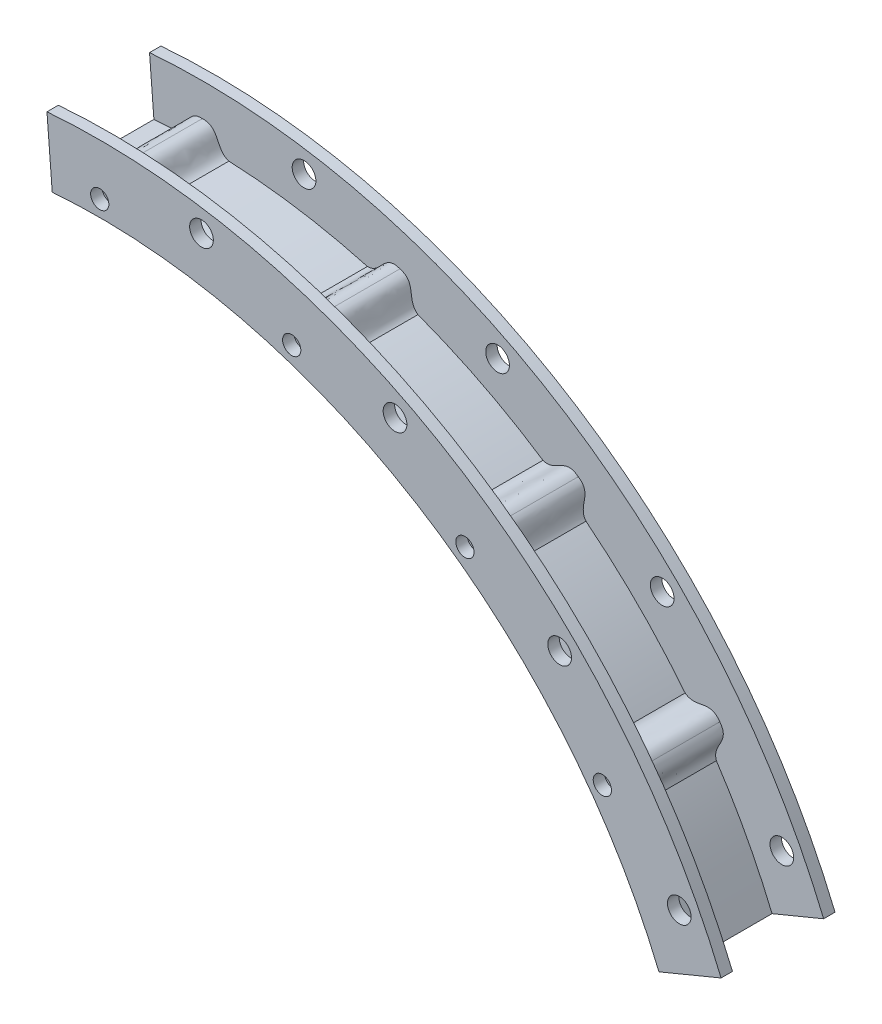
SolidWorks part; units mm, degrees
material "Maple"
ref_plane "Wasteboard" through (0, 0, 0) normal (0, 0, 1) x (1, 0, 0)
ref_plane "Left-Right" through (0, 0, 0) normal (0, 1, 0) x (1, 0, 0)
ref_plane "Front-Back" through (0, 0, 0) normal (1, 0, 0) x (0, 0, -1)
sketch "Sketch2" plane through (0, 0, 0) normal (0, 0, 1) x (1, 0, 0)
  circle A0 centre (0, 0) radius 192.0875 construction
  circle A1 centre (0, 0) radius 209.55 construction
  circle A2 centre (0, 0) radius 171.831 construction
  circle A3 centre (0, 0) radius 252.73 construction
  circle A4 centre (0, 0) radius 184.531 construction
  circle A5 centre (0, 0) radius 187.3885
  circle A6 centre (0, 0) radius 168.656
  dimension "D1" = 384.175
  dimension "D2" = 419.1
  dimension "D3" = 343.662
  dimension "D4" = 505.46
  dimension "D5" = 369.062
  dimension "D6" = 374.777
  dimension "D7" = 337.312
extrude "Boss-Extrude1" add sketch "Sketch2" along normal blind 3.175
sketch "Sketch3" plane through (0, 0, 3.175) normal (0, 0, 1) x (1, 0, 0)
  circle A0 centre (0, 0) radius 171.831
  circle A1 centre (0, 0) radius 168.656
  dimension "D1" = 343.662
extrude "Boss-Extrude2" add sketch "Sketch3" along normal blind 25.4
sketch "Sketch4" plane through (0, 0, 28.575) normal (0, 0, 1) x (1, 0, 0)
  circle A0 centre (0, 0) radius 187.3885
  circle A1 centre (0, 0) radius 168.656
extrude "Boss-Extrude3" add sketch "Sketch4" along normal blind 3.175
sketch "Sketch5" plane through (0, 0, 31.75) normal (0, 0, 1) x (1, 0, 0)
  line L0 (0, 0) -> (0, 196.8159) construction
  line L1 (-7.405, 171.6714) -> (7.405, 171.6714)
  line L2 (0, 178.2342) -> (22.1091, 178.2342) construction
  line L3 (50.9118, 162.6825) -> (45.3645, 143.4767) construction
  line L4 (46.0068, 165.5574) -> (60.092, 160.9809)
  line L5 (94.9151, 143.2376) -> (106.8967, 134.5325)
  line L6 (134.5325, 106.8967) -> (143.2376, 94.9151)
  line L7 (160.9809, 60.092) -> (165.5574, 46.0068)
  line L8 (171.6714, 7.405) -> (171.6714, -7.405)
  line L9 (165.5574, -46.0068) -> (160.9809, -60.092)
  line L10 (143.2376, -94.9151) -> (134.5325, -106.8967)
  line L11 (106.8967, -134.5325) -> (94.9151, -143.2376)
  line L12 (60.092, -160.9809) -> (46.0068, -165.5574)
  line L13 (7.405, -171.6714) -> (-7.405, -171.6714)
  line L14 (-46.0068, -165.5574) -> (-60.092, -160.9809)
  line L15 (-94.9151, -143.2376) -> (-106.8967, -134.5325)
  line L16 (-134.5325, -106.8967) -> (-143.2376, -94.9151)
  line L17 (-160.9809, -60.092) -> (-165.5574, -46.0068)
  line L18 (-171.6714, -7.405) -> (-171.6714, 7.405)
  line L19 (-165.5574, 46.0068) -> (-160.9809, 60.092)
  line L20 (-143.2376, 94.9151) -> (-134.5325, 106.8967)
  line L21 (-106.8967, 134.5325) -> (-94.9151, 143.2376)
  line L22 (-60.092, 160.9809) -> (-46.0068, 165.5574)
  circle A0 centre (0, 0) radius 171.831 construction
  circle A1 centre (0, 173.101) radius 1.27
  circle A3 centre (53.4912, 164.6288) radius 1.27
  circle A4 centre (101.7462, 140.0417) radius 1.27
  circle A5 centre (140.0417, 101.7462) radius 1.27
  circle A6 centre (164.6288, 53.4912) radius 1.27
  circle A7 centre (173.101, 0) radius 1.27
  circle A8 centre (164.6288, -53.4912) radius 1.27
  circle A9 centre (140.0417, -101.7462) radius 1.27
  circle A10 centre (101.7462, -140.0417) radius 1.27
  circle A11 centre (53.4912, -164.6288) radius 1.27
  circle A12 centre (0, -173.101) radius 1.27
  circle A13 centre (-53.4912, -164.6288) radius 1.27
  circle A14 centre (-101.7462, -140.0417) radius 1.27
  circle A15 centre (-140.0417, -101.7462) radius 1.27
  circle A16 centre (-164.6288, -53.4912) radius 1.27
  circle A17 centre (-173.101, 0) radius 1.27
  circle A18 centre (-164.6288, 53.4912) radius 1.27
  circle A19 centre (-140.0417, 101.7462) radius 1.27
  circle A20 centre (-101.7462, 140.0417) radius 1.27
  circle A21 centre (-53.4912, 164.6288) radius 1.27
  spline S0 degree 3 poles (0, 178.2342) (4.9619, 178.4345) (3.6283, 172.828) (7.405, 171.6714) knots 0 0 0 0 1 1 1 1
  spline S1 degree 3 poles (0, 178.2342) (-4.9619, 178.4345) (-3.6283, 172.828) (-7.405, 171.6714) knots 0 0 0 0 1 1 1 1
  spline S2 degree 3 poles (55.0774, 169.5108) (59.8584, 168.1679) (56.8575, 163.248) (60.092, 160.9809) knots 0 0 0 0 1 1 1 1
  spline S3 degree 3 poles (55.0774, 169.5108) (50.4202, 171.2346) (49.9561, 165.4904) (46.0068, 165.5574) knots 0 0 0 0 1 1 1 1
  spline S4 degree 3 poles (104.7634, 144.1945) (108.8954, 141.44) (104.5211, 137.6882) (106.8967, 134.5325) knots 0 0 0 0 1 1 1 1
  spline S5 degree 3 poles (104.7634, 144.1945) (100.8669, 147.2731) (98.6504, 141.9535) (94.9151, 143.2376) knots 0 0 0 0 1 1 1 1
  spline S6 degree 3 poles (144.1945, 104.7634) (147.2731, 100.8669) (141.9535, 98.6504) (143.2376, 94.9151) knots 0 0 0 0 1 1 1 1
  spline S7 degree 3 poles (144.1945, 104.7634) (141.44, 108.8954) (137.6882, 104.5211) (134.5325, 106.8967) knots 0 0 0 0 1 1 1 1
  spline S8 degree 3 poles (169.5108, 55.0774) (171.2346, 50.4202) (165.4904, 49.9561) (165.5574, 46.0068) knots 0 0 0 0 1 1 1 1
  spline S9 degree 3 poles (169.5108, 55.0774) (168.1679, 59.8584) (163.248, 56.8575) (160.9809, 60.092) knots 0 0 0 0 1 1 1 1
  spline S10 degree 3 poles (178.2342, 0) (178.4345, -4.9619) (172.828, -3.6283) (171.6714, -7.405) knots 0 0 0 0 1 1 1 1
  spline S11 degree 3 poles (178.2342, 0) (178.4345, 4.9619) (172.828, 3.6283) (171.6714, 7.405) knots 0 0 0 0 1 1 1 1
  spline S12 degree 3 poles (169.5108, -55.0774) (168.1679, -59.8584) (163.248, -56.8575) (160.9809, -60.092) knots 0 0 0 0 1 1 1 1
  spline S13 degree 3 poles (169.5108, -55.0774) (171.2346, -50.4202) (165.4904, -49.9561) (165.5574, -46.0068) knots 0 0 0 0 1 1 1 1
  spline S14 degree 3 poles (144.1945, -104.7634) (141.44, -108.8954) (137.6882, -104.5211) (134.5325, -106.8967) knots 0 0 0 0 1 1 1 1
  spline S15 degree 3 poles (144.1945, -104.7634) (147.2731, -100.8669) (141.9535, -98.6504) (143.2376, -94.9151) knots 0 0 0 0 1 1 1 1
  spline S16 degree 3 poles (104.7634, -144.1945) (100.8669, -147.2731) (98.6504, -141.9535) (94.9151, -143.2376) knots 0 0 0 0 1 1 1 1
  spline S17 degree 3 poles (104.7634, -144.1945) (108.8954, -141.44) (104.5211, -137.6882) (106.8967, -134.5325) knots 0 0 0 0 1 1 1 1
  spline S18 degree 3 poles (55.0774, -169.5108) (50.4202, -171.2346) (49.9561, -165.4904) (46.0068, -165.5574) knots 0 0 0 0 1 1 1 1
  spline S19 degree 3 poles (55.0774, -169.5108) (59.8584, -168.1679) (56.8575, -163.248) (60.092, -160.9809) knots 0 0 0 0 1 1 1 1
  spline S20 degree 3 poles (0, -178.2342) (-4.9619, -178.4345) (-3.6283, -172.828) (-7.405, -171.6714) knots 0 0 0 0 1 1 1 1
  spline S21 degree 3 poles (0, -178.2342) (4.9619, -178.4345) (3.6283, -172.828) (7.405, -171.6714) knots 0 0 0 0 1 1 1 1
  spline S22 degree 3 poles (-55.0774, -169.5108) (-59.8584, -168.1679) (-56.8575, -163.248) (-60.092, -160.9809) knots 0 0 0 0 1 1 1 1
  spline S23 degree 3 poles (-55.0774, -169.5108) (-50.4202, -171.2346) (-49.9561, -165.4904) (-46.0068, -165.5574) knots 0 0 0 0 1 1 1 1
  spline S24 degree 3 poles (-104.7634, -144.1945) (-108.8954, -141.44) (-104.5211, -137.6882) (-106.8967, -134.5325) knots 0 0 0 0 1 1 1 1
  spline S25 degree 3 poles (-104.7634, -144.1945) (-100.8669, -147.2731) (-98.6504, -141.9535) (-94.9151, -143.2376) knots 0 0 0 0 1 1 1 1
  spline S26 degree 3 poles (-144.1945, -104.7634) (-147.2731, -100.8669) (-141.9535, -98.6504) (-143.2376, -94.9151) knots 0 0 0 0 1 1 1 1
  spline S27 degree 3 poles (-144.1945, -104.7634) (-141.44, -108.8954) (-137.6882, -104.5211) (-134.5325, -106.8967) knots 0 0 0 0 1 1 1 1
  spline S28 degree 3 poles (-169.5108, -55.0774) (-171.2346, -50.4202) (-165.4904, -49.9561) (-165.5574, -46.0068) knots 0 0 0 0 1 1 1 1
  spline S29 degree 3 poles (-169.5108, -55.0774) (-168.1679, -59.8584) (-163.248, -56.8575) (-160.9809, -60.092) knots 0 0 0 0 1 1 1 1
  spline S30 degree 3 poles (-178.2342, 0) (-178.4345, 4.9619) (-172.828, 3.6283) (-171.6714, 7.405) knots 0 0 0 0 1 1 1 1
  spline S31 degree 3 poles (-178.2342, 0) (-178.4345, -4.9619) (-172.828, -3.6283) (-171.6714, -7.405) knots 0 0 0 0 1 1 1 1
  spline S32 degree 3 poles (-169.5108, 55.0774) (-168.1679, 59.8584) (-163.248, 56.8575) (-160.9809, 60.092) knots 0 0 0 0 1 1 1 1
  spline S33 degree 3 poles (-169.5108, 55.0774) (-171.2346, 50.4202) (-165.4904, 49.9561) (-165.5574, 46.0068) knots 0 0 0 0 1 1 1 1
  spline S34 degree 3 poles (-144.1945, 104.7634) (-141.44, 108.8954) (-137.6882, 104.5211) (-134.5325, 106.8967) knots 0 0 0 0 1 1 1 1
  spline S35 degree 3 poles (-144.1945, 104.7634) (-147.2731, 100.8669) (-141.9535, 98.6504) (-143.2376, 94.9151) knots 0 0 0 0 1 1 1 1
  spline S36 degree 3 poles (-104.7634, 144.1945) (-100.8669, 147.2731) (-98.6504, 141.9535) (-94.9151, 143.2376) knots 0 0 0 0 1 1 1 1
  spline S37 degree 3 poles (-104.7634, 144.1945) (-108.8954, 141.44) (-104.5211, 137.6882) (-106.8967, 134.5325) knots 0 0 0 0 1 1 1 1
  spline S38 degree 3 poles (-55.0774, 169.5108) (-50.4202, 171.2346) (-49.9561, 165.4904) (-46.0068, 165.5574) knots 0 0 0 0 1 1 1 1
  spline S39 degree 3 poles (-55.0774, 169.5108) (-59.8584, 168.1679) (-56.8575, 163.248) (-60.092, 160.9809) knots 0 0 0 0 1 1 1 1
  point P191 (0, 0)
  dimension "D1" = 2.54
  dimension "D2" = 20
extrude "Boss-Extrude4" add sketch "Sketch5" against normal blind 30.48
sketch "Sketch6" plane through (0, 0, 31.75) normal (0, 0, 1) x (1, 0, 0)
  line L0 (0, 0) -> (0, 196.8159) construction
  circle A1 centre (0, 173.101) radius 2.54
  circle A2 centre (53.4912, 164.6288) radius 2.54
  circle A22 centre (101.7462, 140.0417) radius 2.54
  circle A23 centre (140.0417, 101.7462) radius 2.54
  circle A24 centre (164.6288, 53.4912) radius 2.54
  circle A25 centre (173.101, 0) radius 2.54
  circle A26 centre (164.6288, -53.4912) radius 2.54
  circle A27 centre (140.0417, -101.7462) radius 2.54
  circle A28 centre (101.7462, -140.0417) radius 2.54
  circle A29 centre (53.4912, -164.6288) radius 2.54
  circle A30 centre (0, -173.101) radius 2.54
  circle A31 centre (-53.4912, -164.6288) radius 2.54
  circle A32 centre (-101.7462, -140.0417) radius 2.54
  circle A33 centre (-140.0417, -101.7462) radius 2.54
  circle A34 centre (-164.6288, -53.4912) radius 2.54
  circle A35 centre (-173.101, 0) radius 2.54
  circle A36 centre (-164.6288, 53.4912) radius 2.54
  circle A37 centre (-140.0417, 101.7462) radius 2.54
  circle A38 centre (-101.7462, 140.0417) radius 2.54
  circle A39 centre (-53.4912, 164.6288) radius 2.54
  point P45 (0, 0)
  point P191 (0, 0)
  dimension "D1" = 5.08
  dimension "D2" = 20
extrude "Cut-Extrude3" cut sketch "Sketch6" against normal blind 3.175
sketch "Sketch7" plane through (0, 0, 31.75) normal (0, 0, 1) x (1, 0, 0)
  line L0 (0, 0) -> (0, 203.459) construction
  circle A0 centre (28.3505, 178.9978) radius 3.302
  circle A2 centre (82.2762, 161.4762) radius 3.302
  circle A3 centre (128.1483, 128.1483) radius 3.302
  circle A4 centre (161.4762, 82.2762) radius 3.302
  circle A5 centre (178.9978, 28.3505) radius 3.302
  circle A6 centre (178.9978, -28.3505) radius 3.302
  circle A7 centre (161.4762, -82.2762) radius 3.302
  circle A8 centre (128.1483, -128.1483) radius 3.302
  circle A9 centre (82.2762, -161.4762) radius 3.302
  circle A10 centre (28.3505, -178.9978) radius 3.302
  circle A11 centre (-28.3505, -178.9978) radius 3.302
  circle A12 centre (-82.2762, -161.4762) radius 3.302
  circle A13 centre (-128.1483, -128.1483) radius 3.302
  circle A14 centre (-161.4762, -82.2762) radius 3.302
  circle A15 centre (-178.9978, -28.3505) radius 3.302
  circle A16 centre (-178.9978, 28.3505) radius 3.302
  circle A17 centre (-161.4762, 82.2762) radius 3.302
  circle A18 centre (-128.1483, 128.1483) radius 3.302
  circle A19 centre (-82.2762, 161.4762) radius 3.302
  circle A20 centre (-28.3505, 178.9978) radius 3.302
  point P45 (0, 0)
  dimension "D1" = 6.604
  dimension "D2" = 20
extrude "Cut-Extrude4" cut sketch "Sketch7" against normal through all
sketch "Sketch8" plane through (0, 0, 31.75) normal (0, 0, 1) x (1, 0, 0)
  line L0 (0, 0) -> (-17.0849, 217.0845)
  line L1 (0, 0) -> (201.1801, 83.3315)
  point P7 (0, 0)
  dimension "D1" = 2
split "Split1" trim tools "Sketch8" bodies to split 132 resulting bodies 133
ref_plane "Plane1" through (0, 0, 28.575) normal (0, 0, -1) x (-1, 0, 0)
split "Split2" trim tools "Plane1" bodies to split 133 resulting bodies 134 135
